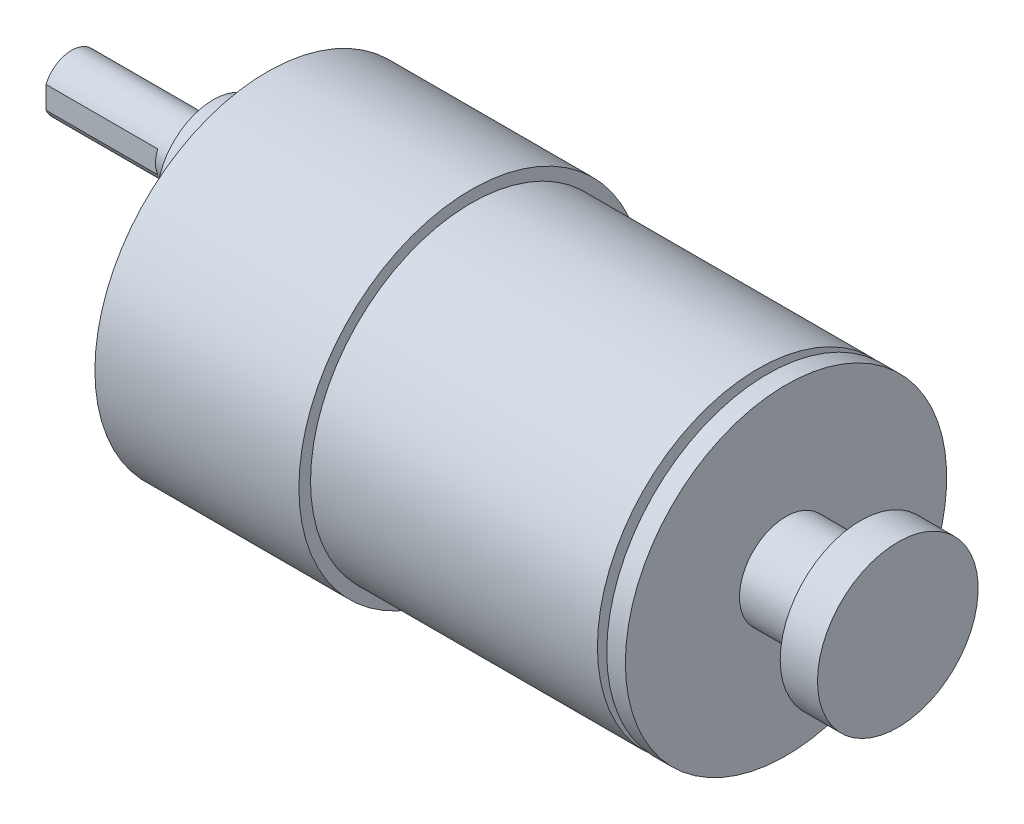
SolidWorks part; units mm, degrees
ref_plane "Front Plane" through (0, 0, 0) normal (0, 0, 1) x (1, 0, 0)
ref_plane "Top Plane" through (0, 0, 0) normal (0, 1, 0) x (1, 0, 0)
ref_plane "Right Plane" through (0, 0, 0) normal (1, 0, 0) x (0, 0, -1)
sketch "Sketch1" plane through (0, 0, 0) normal (0, 0, 1) x (1, 0, 0)
  line L0 (-80.1114, 0) -> (59.0183, 0) construction
  line L1 (0, 0) -> (0, 8.625)
  line L2 (0, 8.625) -> (-4, 8.625)
  line L3 (-4, 8.625) -> (-4, 5)
  line L4 (-4, 5) -> (-12, 5)
  line L5 (-12, 5) -> (-12, 17.25)
  line L6 (-12, 17.25) -> (-14, 17.25)
  line L7 (-14, 17.25) -> (-14, 5)
  line L8 (-14, 5) -> (-15, 5)
  line L9 (-15, 5) -> (-15, 17.25)
  line L10 (-15, 17.25) -> (-45.8, 17.25)
  line L11 (-45.8, 17.25) -> (-45.8, 18.5)
  line L12 (-45.8, 18.5) -> (-67.7, 18.5)
  line L13 (-67.7, 18.5) -> (-67.7, 0)
  line L14 (-67.7, 0) -> (0, 0)
  dimension "D1" = 34.5
  dimension "D2" = 30.8
  dimension "D3" = 37
  dimension "D4" = 21.9
  dimension "D5" = 15
  dimension "D6" = 17.25
  dimension "D7" = 1
  dimension "D8" = 2
  dimension "D9" = 10
  dimension "D10" = 4
revolve "MainBody" add sketch "Sketch1" angle 360 about L0
sketch "Sketch3" plane through (0, 0, 0) normal (0, 0, 1) x (1, 0, 0)
  line L0 (0, 0) -> (-101.2302, 0) construction
  line L1 (0, 7) -> (-101.2302, 7) construction
  line L2 (-67.7, 7) -> (-67.7, 13)
  line L4 (-67.7, 18.5) -> (-67.7, -18.5) construction
  line L5 (-67.7, 13) -> (-73.5, 13)
  line L6 (-73.5, 13) -> (-73.5, 10)
  line L7 (-73.5, 10) -> (-88.7, 10)
  line L8 (-88.7, 10) -> (-88.7, 7)
  line L9 (-88.7, 7) -> (-67.7, 7)
  dimension "D2" = 12
  dimension "D3" = 6
  dimension "D4" = 5.8
  dimension "D5" = 21
  dimension "D1" = 7
revolve "SmallBoss" add sketch "Sketch3" angle 360 about L1
sketch "Sketch4" plane through (-88.7, 0, 0) normal (-1, 0, 0) x (0, 0, 1)
  line L1 (-2.75, 10.7731) -> (2.75, 10.7731)
  line L2 (-2.75, 10.7731) -> (-2.75, 3.2269)
  line L3 (-2.75, 3.2269) -> (2.75, 3.2269)
  line L4 (2.75, 10.7731) -> (2.75, 3.2269)
  line L5 (-2.75, 10.7731) -> (2.75, 3.2269) construction
  line L6 (-2.75, 3.2269) -> (2.75, 10.7731) construction
  circle A0 centre (0, 7) radius 3 construction
  circle A1 centre (0, 7) radius 3
  point P0 (0, 7)
  point P1 (0, 7)
  circle M5 centre (0, 7) radius 3
  dimension "D1" = 5.5
extrude "Cut-Extrude1" cut sketch "Sketch4" against normal blind 12 contours L2 M5 | L4 M5
hole_wizard "M3x0.5 Tapped Hole1" positions "Sketch7" profile "Sketch8" tap size "M3x0.5" standard "ANSI Metric"
sketch "Sketch7" plane through (-67.7, 0, 0) normal (-1, 0, 0) x (0, 0, 1)
  circle A0 centre (0, 0) radius 15.5 construction
  point P5 (15.5, 0)
  point P11 (7.75, -13.4234)
  point P12 (-7.75, -13.4234)
  point P13 (-15.5, 0)
  point P14 (-7.75, 13.4234)
  point P15 (7.75, 13.4234)
  dimension "D1" = 31
  dimension "D2" = 6
sketch "Sketch8" plane through (-67.7, 13.4234, 7.75) normal (0, 1, 0) x (0, 0, 1)
  line L0 (0, 0) -> (0, 9.2511)
  line L1 (0, 9.2511) -> (1.25, 8.5)
  line L2 (1.25, 8.5) -> (1.25, 0)
  line L5 (1.25, 0) -> (0, 0)
  line L10 (0, 9.2511) -> (-1.25, 8.5) construction
  line L11 (0, -6.35) -> (0, 107.95) construction
  dimension "Tap Drill Dia." = 2.5
  dimension "Tap Drill Depth" = 8.5
  dimension "Drill Angle" = 118
cosmetic thread "Hole Thread1" parameters "D1"=6, "D2"=3
cosmetic thread "Hole Thread2" parameters "D1"=6, "D2"=3
cosmetic thread "Hole Thread3" parameters "D1"=6, "D2"=3
cosmetic thread "Hole Thread4" parameters "D1"=6, "D2"=3
cosmetic thread "Hole Thread5" parameters "D1"=6, "D2"=3
cosmetic thread "Hole Thread6" parameters "D1"=6, "D2"=3
sketch "Sketch9" plane through (-67.7, 0, 0) normal (-1, 0, 0) x (0, 0, 1)
  circle A0 centre (0, 0) radius 11.3016
  circle A1 centre (0, 7) radius 9.3451
extrude "Cut-Extrude2" cut sketch "Sketch9" against normal blind 2 contours A1 A0
